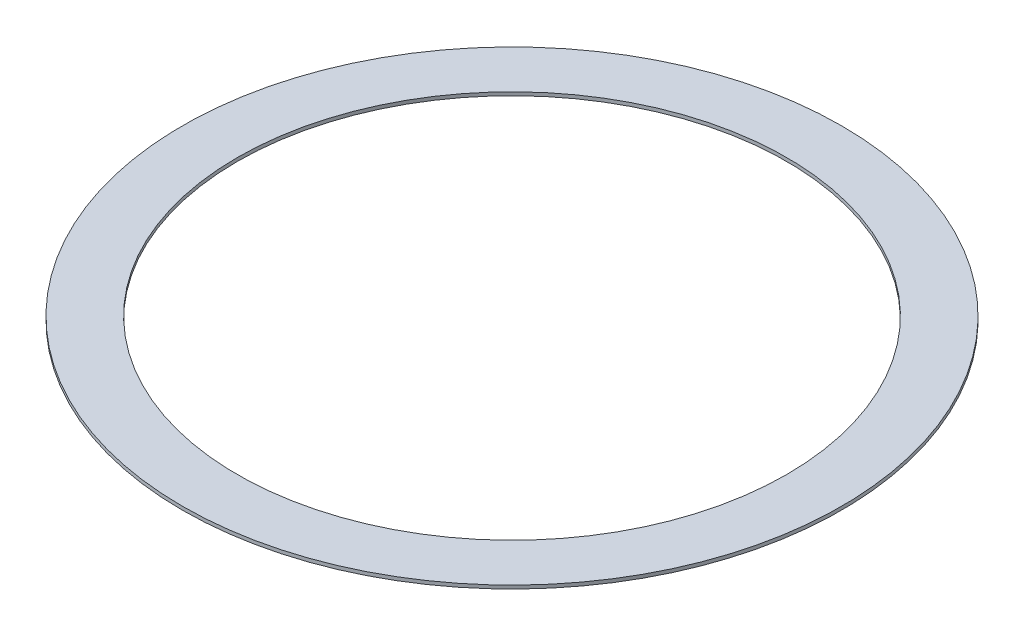
SolidWorks part; units mm, degrees
material "AISI 316 Chapa de acero inoxidable (SS)"
ref_plane "Alzado" through (0, 0, 0) normal (0, 0, 1) x (1, 0, 0)
ref_plane "Planta" through (0, 0, 0) normal (0, 1, 0) x (1, 0, 0)
ref_plane "Vista lateral" through (0, 0, 0) normal (1, 0, 0) x (0, 0, -1)
sketch "Croquis1" plane through (0, 0, 0) normal (0, 1, 0) x (1, 0, 0)
  circle A0 centre (0, 0) radius 48
  dimension "D1" = 96
extrude "Extruir-Lámina1" add sketch "Croquis1" along normal blind 0.5 thin thin type one direction reverse wall 8
